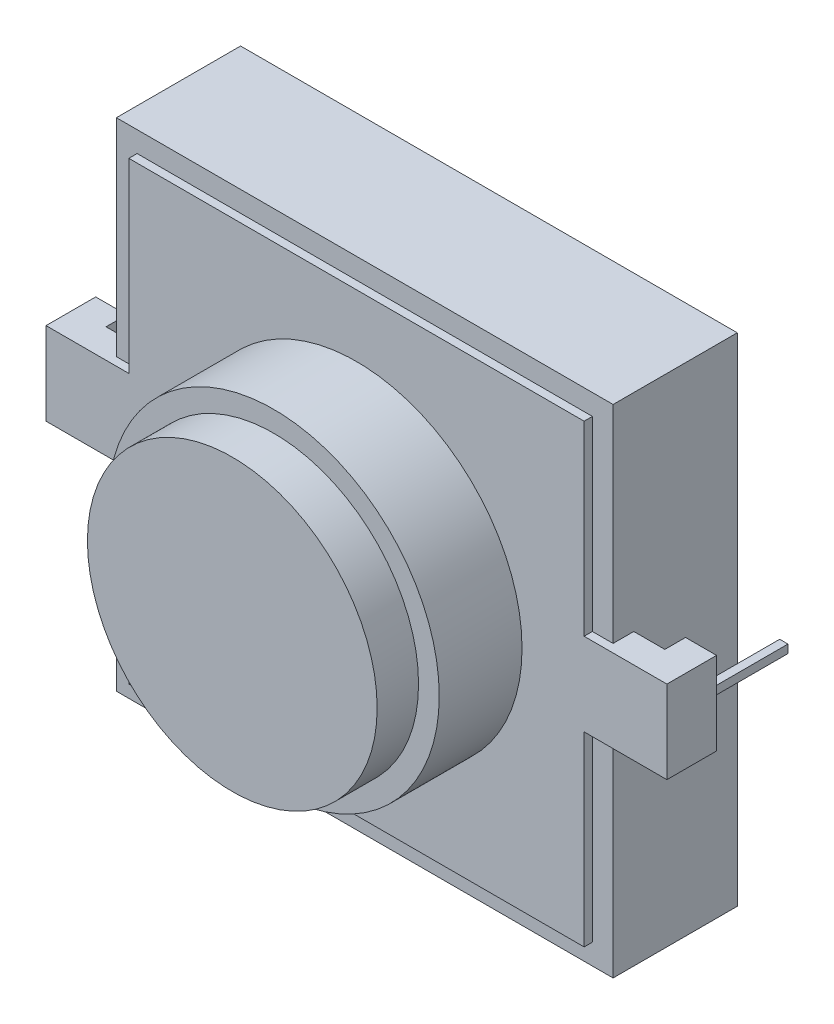
SolidWorks part; units mm, degrees
ref_plane "Plan de face" through (0, 0, 0) normal (0, 0, 1) x (1, 0, 0)
ref_plane "Plan de dessus" through (0, 0, 0) normal (0, 1, 0) x (1, 0, 0)
ref_plane "Plan de droite" through (0, 0, 0) normal (1, 0, 0) x (0, 0, -1)
sketch "Esquisse1" plane through (0, 0, 0) normal (0, 0, 1) x (1, 0, 0)
  line L1 (-6, 6) -> (6, 6)
  line L2 (-6, 6) -> (-6, -6)
  line L3 (-6, -6) -> (6, -6)
  line L4 (6, 6) -> (6, -6)
  line L5 (-6, 6) -> (6, -6) construction
  line L6 (-6, -6) -> (6, 6) construction
  point P0 (0, 0)
  dimension "D1" = 12
  dimension "D2" = 12
extrude "Boss.-Extru.1" add sketch "Esquisse1" along normal blind 3
sketch "Esquisse2" plane through (0, 0, 3) normal (0, 0, 1) x (1, 0, 0)
  line L0 (-8.0195, 0) -> (8.0809, 0) construction
  line L5 (-5.5, 1) -> (-5.5, 5.5)
  line L7 (0, 6.3216) -> (0, -6.4482) construction
  line L8 (5.5, 1) -> (7.5, 1)
  line L9 (7.5, 1) -> (7.5, -1)
  line L10 (5.5, -1) -> (7.5, -1)
  line L11 (-5.5, -1) -> (-7.5, -1)
  line L12 (-7.5, 1) -> (-7.5, -1)
  line L13 (-5.5, 1) -> (-7.5, 1)
  line L16 (5.5, 5.5) -> (5.5, 1)
  line L17 (5.5, -1) -> (5.5, -5.5)
  line L19 (-5.5, -5.5) -> (-5.5, -1)
  line L20 (-5.5, 5.5) -> (5.5, 5.5)
  line L21 (-5.5, -5.5) -> (5.5, -5.5)
  point P0 (0, 0)
  point P14 (7.5, 0)
  dimension "D1" = 11
  dimension "D2" = 5.5
  dimension "D3" = 1
  dimension "D4" = 2
  dimension "D5" = 5.5
extrude "Boss.-Extru.2" add sketch "Esquisse2" along normal blind 0.2
sketch "Esquisse3" plane through (0, 0, 0) normal (0, 1, 0) x (1, 0, 0)
  line L0 (6, -3) -> (6, -2.5)
  line L1 (6, -3) -> (6, 0) construction
  line L2 (6, -2.5) -> (6.75, -2.5)
  line L3 (6.75, -2.5) -> (6.75, -2)
  line L4 (6.75, -2) -> (7.5, -2)
  line L5 (7.5, -2) -> (7.5, -3)
  line L6 (7.5, -3) -> (6, -3)
  line L7 (0, -4.7016) -> (0, 0.6704) construction
  line L8 (-7.5, -3) -> (-6, -3)
  line L9 (-6, -3) -> (-6, -2.5)
  line L10 (-6, -2.5) -> (-6.75, -2.5)
  line L11 (-6.75, -2.5) -> (-6.75, -2)
  line L12 (-6.75, -2) -> (-7.5, -2)
  line L13 (-7.5, -2) -> (-7.5, -3)
  dimension "D1" = 1
  dimension "D2" = 0.5
  dimension "D3" = 0.75
extrude "Boss.-Extru.3" add sketch "Esquisse3" along normal mid plane 2
sketch "Esquisse4" plane through (0, 0, 0) normal (0, 1, 0) x (1, 0, 0)
  line L0 (7.125, -2) -> (7.125, -5.148) construction
  line L1 (7.5, -2) -> (6.75, -2) construction
  line L2 (7.225, -2) -> (7.225, 0)
  line L3 (7.225, 0) -> (7.025, 0)
  line L4 (7.225, -2) -> (7.025, -2)
  line L5 (7.025, -2) -> (7.025, 0)
  line L6 (0, -4.2342) -> (0, 1.0763) construction
  line L7 (-7.225, 0) -> (-7.025, 0)
  line L8 (-7.025, -2) -> (-7.025, 0)
  line L9 (-7.225, -2) -> (-7.225, 0)
  line L10 (-7.225, -2) -> (-7.025, -2)
  point P8 (7.125, 0)
  dimension "D1" = 0.2
extrude "Boss.-Extru.4" add sketch "Esquisse4" along normal mid plane 0.2
sketch "Esquisse5" plane through (0, 0, 3.2) normal (0, 0, 1) x (1, 0, 0)
  circle A0 centre (0, 0) radius 4
  dimension "D1" = 8
extrude "Boss.-Extru.5" add sketch "Esquisse5" along normal blind 2
sketch "Esquisse6" plane through (0, 0, 5.2) normal (0, 0, 1) x (1, 0, 0)
  circle A0 centre (0, 0) radius 3.5
  dimension "D1" = 7
extrude "Enlèv. mat.-Extru.1" cut sketch "Esquisse6" against normal blind 2
sketch "Esquisse7" plane through (0, 0, 3.2) normal (0, 0, 1) x (1, 0, 0)
  circle A0 centre (0, 0) radius 3.5
  dimension "D1" = 7
extrude "Boss.-Extru.6" add sketch "Esquisse7" along normal blind 3
